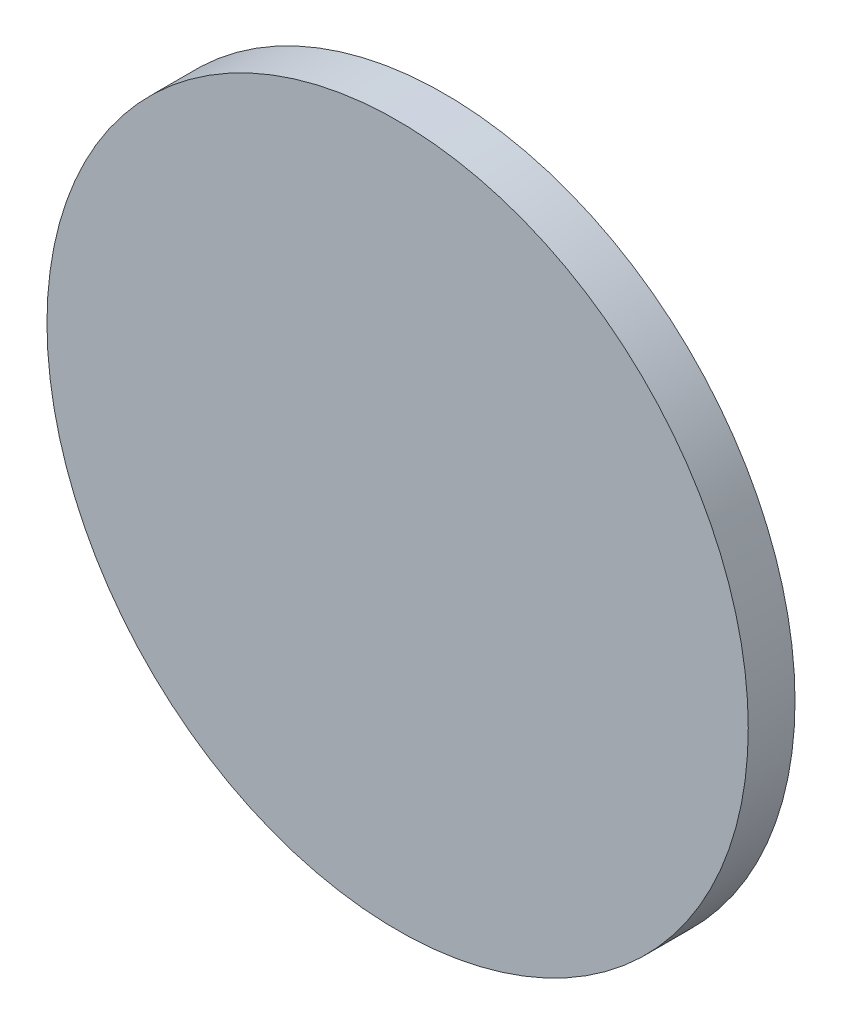
SolidWorks part; units mm, degrees
ref_plane "Front Plane" through (0, 0, 0) normal (0, 0, 1) x (1, 0, 0)
ref_plane "Top Plane" through (0, 0, 0) normal (0, 1, 0) x (1, 0, 0)
ref_plane "Right Plane" through (0, 0, 0) normal (1, 0, 0) x (0, 0, -1)
sketch "Sketch1" plane through (0, 0, 0) normal (0, 0, 1) x (1, 0, 0)
  circle A0 centre (0, 0) radius 37.5
  point P3 (0, 0)
  dimension "D1" = 75
extrude "Boss-Extrude1" add sketch "Sketch1" along normal blind 5
sketch "Sketch2" plane through (0, 0, 0) normal (0, 0, -1) x (-1, 0, 0)
  circle A0 centre (0, 36.25) radius 1.2613
  circle A1 centre (0, 0) radius 37.5 construction
  dimension "D1" = 36.25
